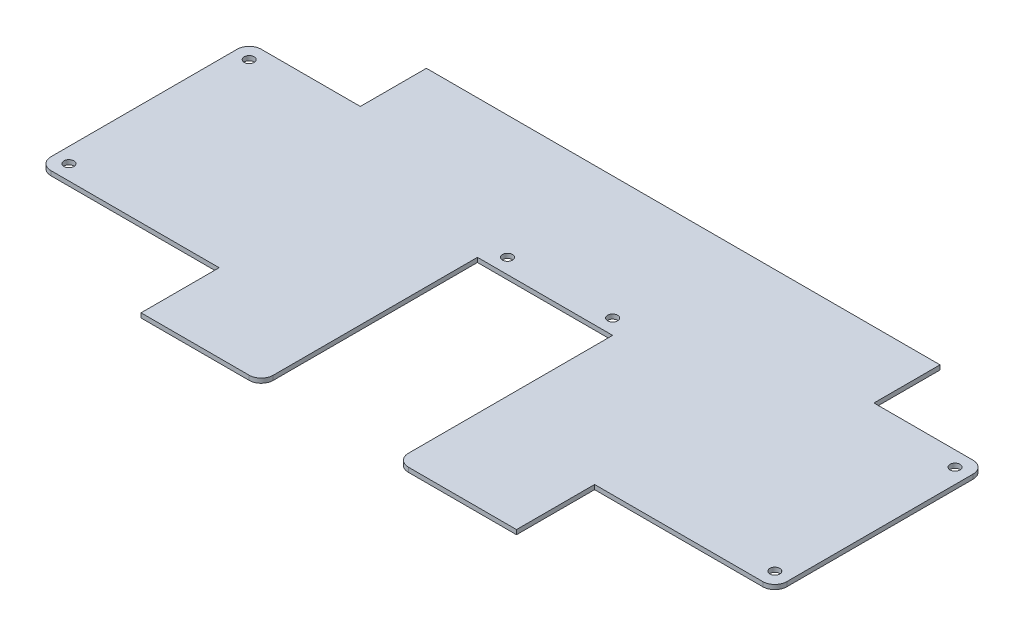
SolidWorks part; units mm, degrees
material "ABS PC"
ref_plane "Front Plane" through (0, 0, 0) normal (0, 0, 1) x (1, 0, 0)
ref_plane "Top Plane" through (0, 0, 0) normal (0, 1, 0) x (1, 0, 0)
ref_plane "Right Plane" through (0, 0, 0) normal (1, 0, 0) x (0, 0, -1)
sketch "Sketch1" plane through (0, 0, 0) normal (0, 1, 0) x (1, 0, 0)
  line L1 (0, 0) -> (245, 0)
  line L2 (0, 0) -> (0, 118)
  line L3 (0, 118) -> (245, 118)
  line L4 (245, 0) -> (245, 118)
  dimension "D1" = 245
  dimension "D2" = 118
extrude "Boss-Extrude1" add sketch "Sketch1" along normal blind 1.5
sketch "Sketch2" plane through (0, 1.5, 0) normal (0, 1, 0) x (1, 0, 0)
  line L1 (0, 118) -> (37, 118)
  line L2 (0, 118) -> (0, 96)
  line L3 (0, 96) -> (37, 96)
  line L4 (37, 118) -> (37, 96)
  line L5 (0, 0) -> (60, 0)
  line L6 (0, 0) -> (0, 26)
  line L7 (0, 26) -> (60, 26)
  line L8 (60, 0) -> (60, 26)
  line L9 (245, 118) -> (208, 118)
  line L10 (245, 118) -> (245, 96)
  line L11 (245, 96) -> (208, 96)
  line L12 (208, 118) -> (208, 96)
  line L13 (245, 0) -> (185, 0)
  line L14 (245, 0) -> (245, 26)
  line L15 (245, 26) -> (185, 26)
  line L16 (185, 0) -> (185, 26)
  line L17 (100, 0) -> (145, 0)
  line L18 (100, 0) -> (100, 72)
  line L19 (100, 72) -> (145, 72)
  line L20 (145, 0) -> (145, 72)
  dimension "D1" = 37
  dimension "D2" = 22
  dimension "D3" = 26
  dimension "D4" = 37
  dimension "D5" = 60
  dimension "D6" = 60
  dimension "D7" = 26
  dimension "D8" = 22
  dimension "D9" = 100
  dimension "D10" = 100
  dimension "D11" = 72
extrude "Cut-Extrude1" cut sketch "Sketch2" against normal through all
sketch "Sketch3" plane through (0, 0, 0) normal (0, -1, 0) x (1, 0, 0)
  line L0 (60, -26) -> (0, -26) construction
  line L1 (0, -96) -> (0, -26) construction
  line L2 (0, -96) -> (37, -96) construction
  line L6 (100, -72) -> (100, 0) construction
  line L8 (145, -72) -> (100, -72) construction
  line L9 (145, 0) -> (145, -72) construction
  line L10 (245, -26) -> (185, -26) construction
  circle A0 centre (5, -31) radius 1.65
  circle A1 centre (5, -91) radius 1.65
  circle A8 centre (240, -31) radius 1.65
  circle A9 centre (240, -91) radius 1.65
  circle A10 centre (105, -77) radius 1.65
  circle A11 centre (140, -77) radius 1.65
  dimension "D1" = 3.3
  dimension "D6" = 3.3
  dimension "D7" = 5
  dimension "D11" = 5
  dimension "D8" = 3.3
  dimension "D10" = 3.3
  dimension "D2" = 5
  dimension "D3" = 5
  dimension "D4" = 5
  dimension "D5" = 5
  dimension "D9" = 5
  dimension "D12" = 5
extrude "Cut-Extrude2" cut sketch "Sketch3" against normal blind 10
fillet "Fillet1" radius 4 6 edges at (100, 0.75, 0) (145, 0.75, 0) (245, 0.75, -26) (245, 0.75, -96) (0, 0.75, -26) (0, 0.75, -96)
